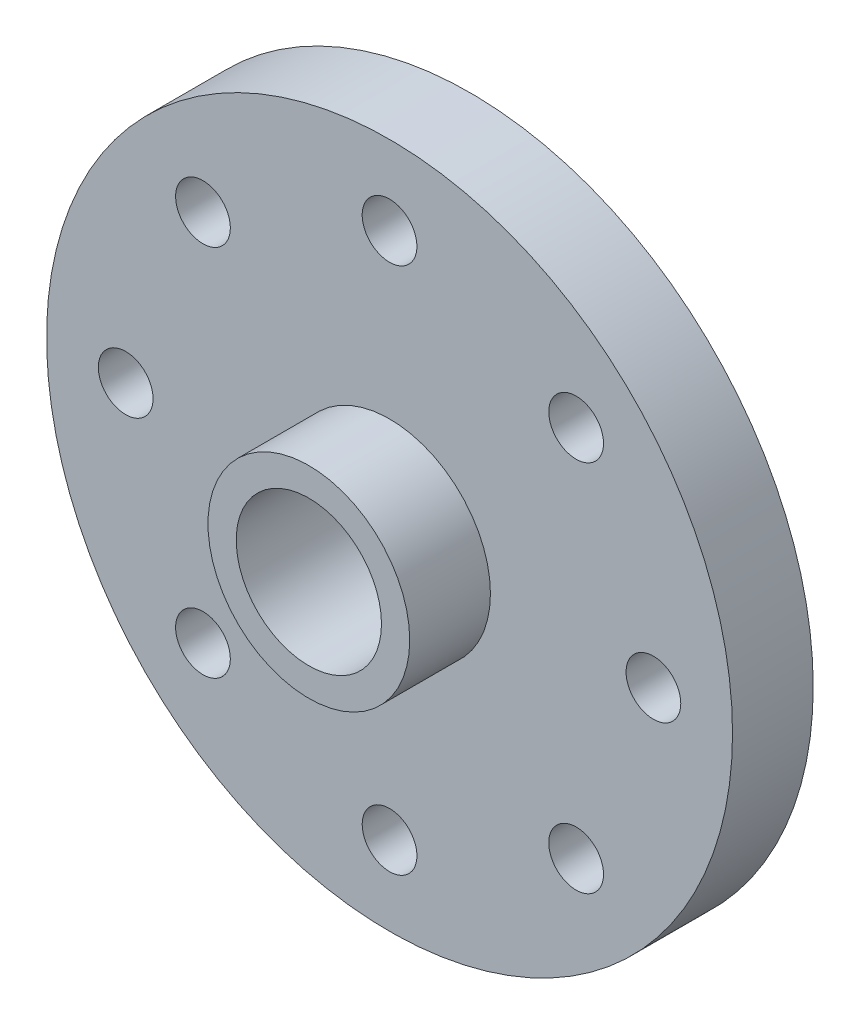
SolidWorks part; units mm, degrees
ref_plane "Front Plane" through (0, 0, 0) normal (0, 0, 1) x (1, 0, 0)
ref_plane "Top Plane" through (0, 0, 0) normal (0, 1, 0) x (1, 0, 0)
ref_plane "Right Plane" through (0, 0, 0) normal (1, 0, 0) x (0, 0, -1)
sketch "Sketch1" plane through (0, 0, 0) normal (0, 0, 1) x (1, 0, 0)
  circle A0 centre (0, 0) radius 42.5
  dimension "D1" = 85
extrude "Boss-Extrude1" add sketch "Sketch1" along normal blind 10
sketch "Sketch2" plane through (0, 0, 10) normal (0, 0, 1) x (1, 0, 0)
  circle A0 centre (0, 0) radius 12.5
  dimension "D1" = 25
extrude "Boss-Extrude2" add sketch "Sketch2" along normal blind 10
sketch "Sketch3" plane through (0, 0, 20) normal (0, 0, 1) x (1, 0, 0)
  circle A0 centre (0, 0) radius 9
  dimension "D1" = 18
extrude "Cut-Extrude1" cut sketch "Sketch3" against normal up to surface (20 mm away) up to face at (42.5, 0, 0)
sketch "Sketch4" plane through (0, 0, 10) normal (0, 0, 1) x (1, 0, 0)
  line L0 (0, 0) -> (0, 42.5) construction
  circle A0 centre (0, 32.6966) radius 3.3909
  circle A2 centre (0, 0) radius 42.5 construction
  point P2 (0, 0)
  point P3 (0, 32.6966)
extrude "Cut-Extrude2" cut sketch "Sketch4" against normal up to surface (10 mm away) up to face at (9, 0, 0)
pattern_circular "CirPattern1" count 8 over 360 about axis through (0, 0, 0) along (0, 0, 1) of "Cut-Extrude2"
